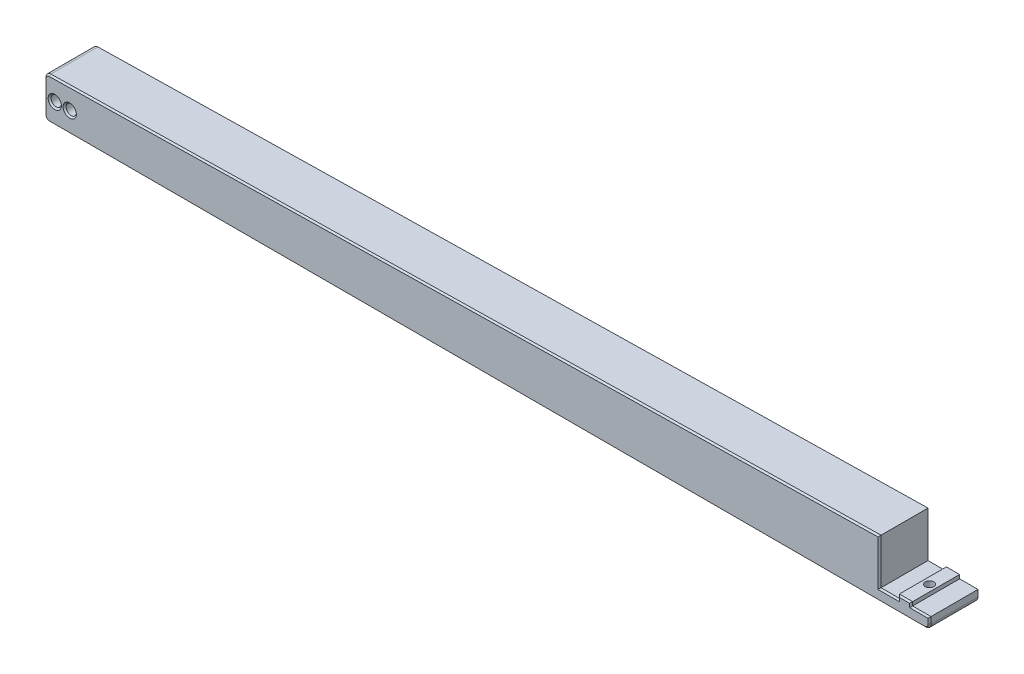
SolidWorks part; units mm, degrees
ref_plane "Front Plane" through (0, 0, 0) normal (0, 0, 1) x (1, 0, 0)
ref_plane "Top Plane" through (0, 0, 0) normal (0, 1, 0) x (1, 0, 0)
ref_plane "Right Plane" through (0, 0, 0) normal (1, 0, 0) x (0, 0, -1)
sketch "Sketch1" plane through (0, 0, 0) normal (0, 0, 1) x (1, 0, 0)
  line L0 (15.2, -92.5791) -> (15.2, -76.0527)
  line L1 (15, -92.5791) -> (15, -87.5791) construction
  line L2 (27.6006, -92.5791) -> (15, -92.5791) construction
  line L3 (15.2, -92.5791) -> (369.3363, -92.5791)
  line L4 (349.3363, -87.94) -> (356.6863, -87.94)
  line L7 (369.3363, -87.94) -> (369.3363, -92.5791)
  line L8 (349.3363, -87.94) -> (349.3363, -69.74)
  line L9 (349.3363, -69.74) -> (15.2, -76.0527)
  line L10 (361.9863, -86.44) -> (361.9863, -87.94)
  line L11 (361.9863, -86.44) -> (356.6863, -86.44)
  line L12 (356.6863, -86.44) -> (356.6863, -87.94)
  line L13 (361.9863, -87.94) -> (369.3363, -87.94)
  line L14 (369.3363, -82.5352) -> (369.3363, -86.14) construction
  line L15 (27.6006, -76.0527) -> (15, -76.0527) construction
  circle A0 centre (25.3003, -84.3159) radius 2.05
  circle A1 centre (19.3003, -84.3159) radius 2.05
  dimension "D2" = 4.1
  dimension "D3" = 4.1
  dimension "D1" = 0.2
extrude "Boss-Extrude1" add sketch "Sketch1" along normal blind 20
sketch "Sketch2" plane through (0, -92.5791, 0) normal (0, -1, 0) x (-1, 0, 0)
  line L0 (-349.3363, 0) -> (-349.3363, -20) construction
  line L3 (-15.2, -20) -> (-369.3363, -20) construction
  line L4 (-349.3363, -69.543) -> (-349.3363, 430.457) construction
  line L5 (-349.3363, 0) -> (-369.3363, -20) construction
  circle A0 centre (-359.3363, -10) radius 1.7
  dimension "D1" = 3.4
extrude "Cut-Extrude1" cut sketch "Sketch2" against normal blind 20
sketch "Sketch3" plane through (0, -92.5791, 0) normal (0, -1, 0) x (1, 0, 0)
  circle A0 centre (359.3363, 10) radius 2.8
  dimension "D1" = 5.6
extrude "Cut-Extrude2" cut sketch "Sketch3" against normal blind 2
fillet "Fillet1" radius 2 3 edges at (369.3363, -92.5791, 10) (15.2, -76.0527, 10) (15.2, -92.5791, 10)
chamfer "Chamfer1" distance 0.6 angle 45 15 edges at (21.3503, -84.3159, 0) (365.6613, -87.94, 0) (361.9863, -87.19, 0) (359.3363, -86.44, 0) (356.6863, -87.19, 0) (353.0113, -87.94, 0) (349.3363, -78.84, 0) (183.2493, -72.8778, 0) (15.7725, -76.6144, 0) (15.2, -84.2971, 0) (15.7858, -91.9933, 0) (192.2681, -92.5791, 0) (368.7505, -91.9933, 0) (369.3363, -89.2595, 0) (27.3503, -84.3159, 0)
chamfer "Chamfer2" distance 0.6 angle 45 15 edges at (21.3503, -84.3159, 20) (27.3503, -84.3159, 20) (15.7858, -91.9933, 20) (15.2, -84.2971, 20) (15.7725, -76.6144, 20) (183.2493, -72.8778, 20) (349.3363, -78.84, 20) (353.0113, -87.94, 20) (356.6863, -87.19, 20) (359.3363, -86.44, 20) (361.9863, -87.19, 20) (365.6613, -87.94, 20) (369.3363, -89.2595, 20) (368.7505, -91.9933, 20) (192.2681, -92.5791, 20)
